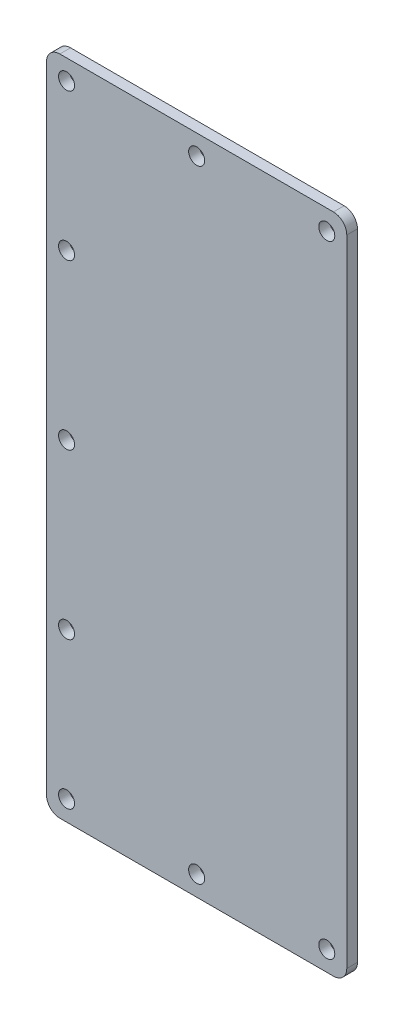
SolidWorks part; units mm, degrees
material "普通碳钢"
ref_plane "前视基准面" through (0, 0, 0) normal (0, 0, 1) x (1, 0, 0)
ref_plane "上视基准面" through (0, 0, 0) normal (0, 1, 0) x (1, 0, 0)
ref_plane "右视基准面" through (0, 0, 0) normal (1, 0, 0) x (0, 0, -1)
sketch "草图1" plane through (0, 0, 0) normal (0, 0, 1) x (1, 0, 0)
  line L1 (10, 0) -> (215, 0)
  line L2 (0, 10) -> (0, 486)
  line L3 (10, 496) -> (215, 496)
  line L4 (225, 10) -> (225, 486)
  arc A0 (215, 0) -> (225, 10) centre (215, 10) ccw
  arc A1 (10, 0) -> (0, 10) centre (10, 10) cw
  arc A2 (215, 496) -> (225, 486) centre (215, 486) cw
  arc A3 (0, 486) -> (10, 496) centre (10, 486) cw
  point P9 (0, 0)
  point P12 (225, 496)
  point P15 (0, 496)
  dimension "D3" = 10
  dimension "D1" = 225
  dimension "D2" = 496
extrude "凸台-拉伸1" add sketch "草图1" along normal blind 8
sketch "草图2" plane through (0, 0, 8) normal (0, 0, 1) x (1, 0, 0)
  line L6 (210, 10) -> (210, 486)
  line L7 (210, 10) -> (210, 486) construction
  line L9 (215, 481) -> (10, 481)
  line L10 (215, 481) -> (10, 481) construction
  line L12 (15, 486) -> (15, 10)
  line L13 (15, 486) -> (15, 10) construction
  line L14 (215, 371) -> (10, 371) construction
  line L15 (10, 15) -> (215, 15)
  line L16 (10, 15) -> (215, 15) construction
  line L17 (10, 125) -> (215, 125) construction
  circle A4 centre (112.5, 481) radius 6
  circle A5 centre (210, 481) radius 6
  circle A6 centre (15, 481) radius 6
  circle A7 centre (15, 15) radius 6
  circle A8 centre (210, 15) radius 6
  circle A9 centre (112.5, 15) radius 6
  circle A10 centre (15, 248) radius 6
  circle A11 centre (15, 371) radius 6
  circle A12 centre (15, 125) radius 6
  dimension "D5" = 110
  dimension "D7" = 12
  dimension "D1" = 15
  dimension "D2" = 15
  dimension "D3" = 15
  dimension "D4" = 15
  dimension "D6" = 110
extrude "切除-拉伸1" cut sketch "草图2" against normal blind 10
